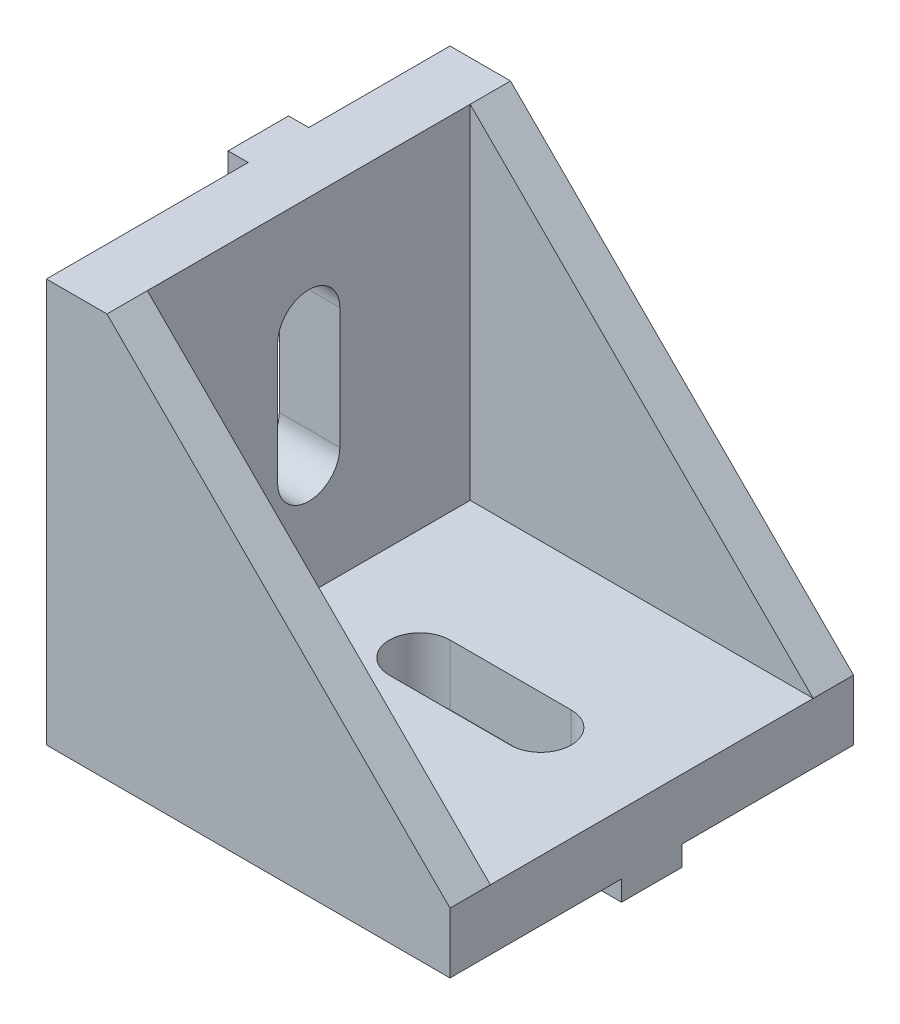
SolidWorks part; units mm, degrees
ref_plane "Alzado" through (0, 0, 0) normal (0, 0, 1) x (1, 0, 0)
ref_plane "Planta" through (0, 0, 0) normal (0, 1, 0) x (1, 0, 0)
ref_plane "Vista lateral" through (0, 0, 0) normal (1, 0, 0) x (0, 0, -1)
sketch "Croquis1" plane through (0, 0, 0) normal (0, 0, 1) x (1, 0, 0)
  line L0 (0, 20) -> (3, 20)
  line L1 (0, 0) -> (20, 0)
  line L2 (0, 0) -> (0, 20)
  line L5 (3, 20) -> (3, 3)
  line L6 (3, 3) -> (20, 3)
  line L7 (20, 3) -> (20, 0)
  dimension "D1" = 20
  dimension "D2" = 20
  dimension "D3" = 3
  dimension "D4" = 3
extrude "Saliente-Extruir1" add sketch "Croquis1" along normal blind 20
sketch "Croquis2" plane through (0, 0, 20) normal (0, 0, 1) x (1, 0, 0)
  line L0 (3, 20) -> (20, 3)
  line L1 (20, 3) -> (20, 0)
  line L2 (20, 0) -> (0, 0)
  line L3 (0, 0) -> (0, 20)
  line L4 (0, 20) -> (3, 20)
extrude "Saliente-Extruir2" add sketch "Croquis2" against normal blind 2
sketch "Croquis3" plane through (0, 0, 0) normal (0, 0, -1) x (-1, 0, 0)
  line L0 (0, 20) -> (-3, 20)
  line L1 (-3, 20) -> (-20, 3)
  line L2 (-20, 3) -> (-20, 0)
  line L3 (-20, 0) -> (0, 0)
  line L4 (0, 0) -> (0, 20)
extrude "Saliente-Extruir3" add sketch "Croquis3" against normal blind 2
sketch "Croquis4" plane through (3, 0, 0) normal (1, 0, 0) x (0, 0, -1)
  line L0 (-18, 20) -> (-2, 3) construction
  line L1 (-2, 3) -> (-2, 20) construction
  line L2 (-2, 20) -> (-18, 3) construction
  line L3 (-11.5, 11.5) -> (-8.5, 11.5)
  line L4 (-10, 8.5) -> (-10, 14.5) construction
  line L5 (-11.5407, 8.5) -> (-11.5407, 14.5)
  line L6 (-8.4593, 8.5) -> (-8.4593, 14.5)
  arc A0 (-11.5407, 8.5) -> (-8.4593, 8.5) centre (-10, 8.5) ccw
  arc A1 (-8.4593, 14.5) -> (-11.5407, 14.5) centre (-10, 14.5) ccw
  point P11 (-10, 11.5)
  point P13 (-10, 11.5)
  dimension "D1" = 6
extrude "Cortar-Extruir1" cut sketch "Croquis4" against normal through all
sketch "Croquis5" plane through (0, 3, 0) normal (0, 1, 0) x (1, 0, 0)
  line L0 (20, -2) -> (3, -18) construction
  line L1 (3, -18) -> (3, -2) construction
  line L2 (3, -2) -> (20, -18) construction
  line L3 (11.5, -11.5) -> (11.5, -8.5)
  line L4 (8.5, -10) -> (14.5, -10) construction
  line L5 (8.5, -8.4921) -> (14.5, -8.4921)
  line L6 (8.5, -11.5079) -> (14.5, -11.5079)
  arc A0 (8.5, -8.4921) -> (8.5, -11.5079) centre (8.5, -10) ccw
  arc A1 (14.5, -11.5079) -> (14.5, -8.4921) centre (14.5, -10) ccw
  point P11 (11.5, -10)
  point P13 (11.5, -10)
  dimension "D1" = 3
  dimension "D2" = 6
extrude "Cortar-Extruir2" cut sketch "Croquis5" against normal through all
sketch "Croquis6" plane through (0, 0, 0) normal (0, -1, 0) x (1, 0, 0)
  line L0 (0, 10) -> (20, 10) construction
  line L1 (0, 20) -> (0, 0) construction
  line L2 (20, 20) -> (20, 0) construction
  line L4 (0, 8.5) -> (1.5, 8.5)
  line L5 (0, 8.5) -> (0, 11.5)
  line L6 (0, 11.5) -> (1.5, 11.5)
  line L7 (1.5, 8.5) -> (1.5, 11.5)
  line L8 (0, 8.5) -> (1.5, 11.5) construction
  line L9 (0, 11.5) -> (1.5, 8.5) construction
  line L10 (18.5, 8.5) -> (20, 8.5)
  line L11 (18.5, 8.5) -> (18.5, 11.5)
  line L12 (18.5, 11.5) -> (20, 11.5)
  line L13 (20, 8.5) -> (20, 11.5)
  line L14 (18.5, 8.5) -> (20, 11.5) construction
  line L15 (18.5, 11.5) -> (20, 8.5) construction
  point P6 (0.75, 10)
  point P11 (19.25, 10)
  dimension "D1" = 1.5
  dimension "D2" = 3
  dimension "D3" = 1.5
  dimension "D4" = 3
extrude "Saliente-Extruir4" add sketch "Croquis6" along normal blind 1
sketch "Croquis7" plane through (0, 0, 0) normal (-1, 0, 0) x (0, 0, 1)
  line L0 (8.5, 20) -> (8.5, 0) construction
  line L1 (20, 20) -> (0, 20) construction
  line L3 (7, 20) -> (10, 20)
  line L4 (7, 20) -> (7, 18.5)
  line L5 (7, 18.5) -> (10, 18.5)
  line L6 (10, 20) -> (10, 18.5)
  line L7 (7, 20) -> (10, 18.5) construction
  line L8 (7, 18.5) -> (10, 20) construction
  line L13 (8.5, 0) -> (10, 0)
  line L14 (8.5, 0) -> (8.5, 1.5)
  line L15 (8.5, 1.5) -> (10, 1.5)
  line L16 (10, 0) -> (10, 1.5)
  point P4 (8.5, 19.25)
  dimension "D1" = 3
  dimension "D2" = 1.5
  dimension "D3" = 1.5
extrude "Saliente-Extruir6" add sketch "Croquis7" along normal blind 1
